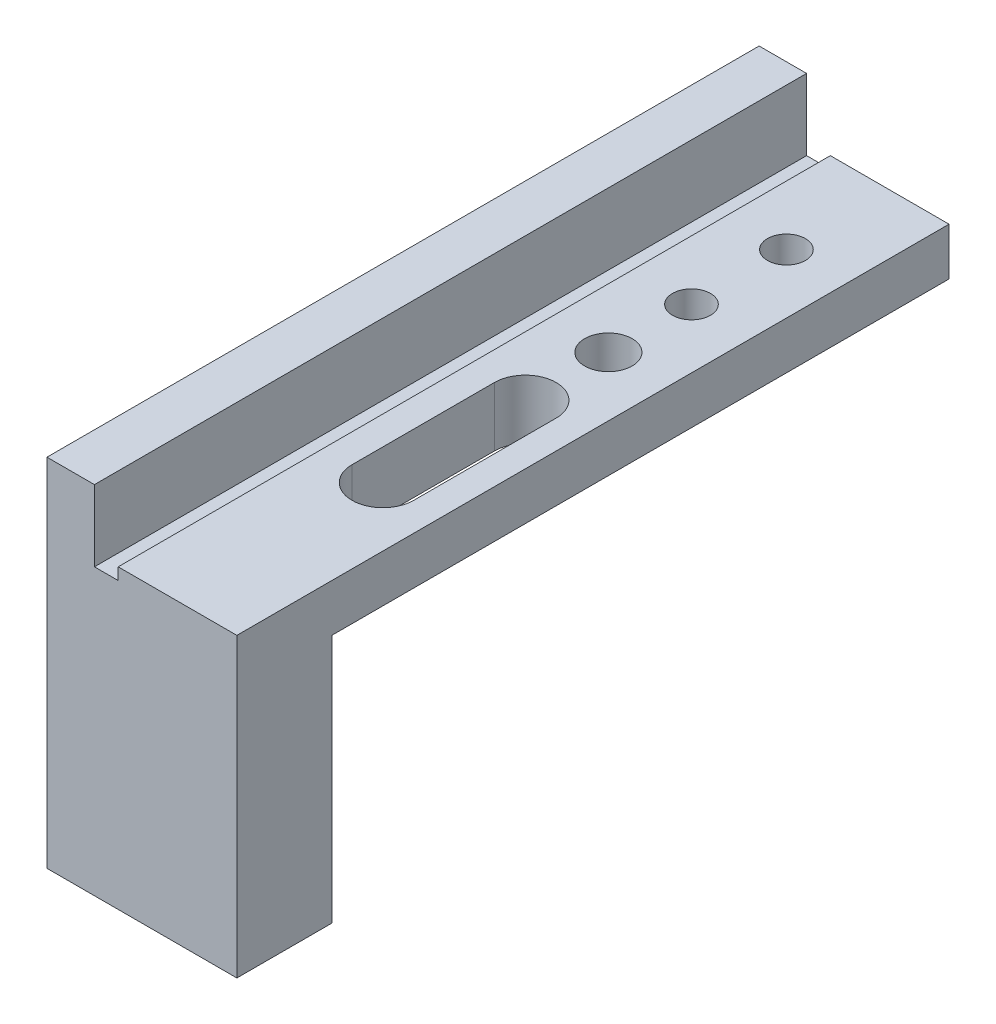
SolidWorks part; units mm, degrees
ref_plane "Front Plane" through (0, 0, 0) normal (0, 0, 1) x (1, 0, 0)
ref_plane "Top Plane" through (0, 0, 0) normal (0, 1, 0) x (1, 0, 0)
ref_plane "Right Plane" through (0, 0, 0) normal (1, 0, 0) x (0, 0, -1)
sketch "Sketch1" plane through (0, 0, 0) normal (0, 0, 1) x (1, 0, 0)
  line L1 (-5.1525, 3) -> (-3.1525, 3)
  line L2 (-5.1525, 3) -> (-5.1525, -2)
  line L4 (-3.1525, 3) -> (-3.1525, 0)
  line L5 (-5.1525, -2) -> (2.8475, -2)
  line L7 (-2.1525, 0.5) -> (2.8475, 0.5)
  line L8 (2.8475, -2) -> (2.8475, 0.5)
  line L9 (-3.1525, 0) -> (-2.1525, 0)
  line L10 (-2.1525, 0) -> (-2.1525, 0.5)
  dimension "D1" = 2
  dimension "D2" = 1
  dimension "D3" = 0.5
  dimension "D4" = 8
  dimension "D5" = 5
  dimension "D6" = 2.5
extrude "Boss-Extrude1" add sketch "Sketch1" along normal blind 30
sketch "Sketch2" plane through (0, -2, 0) normal (0, -1, 0) x (1, 0, 0)
  line L1 (-5.1525, 30) -> (-5.1525, 0) construction
  line L2 (2.8475, 30) -> (-5.1525, 30)
  line L3 (2.8475, 30) -> (2.8475, 26)
  line L4 (2.8475, 26) -> (-5.1525, 26)
  line L5 (-5.1525, 30) -> (-5.1525, 26)
  dimension "D1" = 4
sketch "Sketch3" plane through (0, 0.5, 0) normal (0, 1, 0) x (1, 0, 0)
  line L0 (0.3475, -21.35) -> (0.3475, -15.35) construction
  line L1 (-0.9525, -21.35) -> (-0.9525, -15.35)
  line L2 (1.6475, -21.35) -> (1.6475, -15.35)
  line L4 (-5.1525, -30) -> (-5.1525, 0) construction
  line L5 (2.8475, -30) -> (-2.1525, -30) construction
  circle A0 centre (0.3475, -11.85) radius 1
  arc A1 (-0.9525, -21.35) -> (1.6475, -21.35) centre (0.3475, -21.35) ccw
  arc A2 (1.6475, -15.35) -> (-0.9525, -15.35) centre (0.3475, -15.35) ccw
  point P4 (0.3475, -18.35)
  dimension "D2" = 1.3
  dimension "D6" = 2
  dimension "D1" = 6
  dimension "D3" = 8.65
  dimension "D4" = 5.5
  dimension "D5" = 18.15
extrude "Cut-Extrude1" cut sketch "Sketch3" against normal blind 10
hole_wizard "M2 Tapped Hole1" positions "Sketch4" profile "Sketch5" tap size "M2" standard "ISO"
sketch "Sketch4" plane through (0, 0.5, 0) normal (0, 1, 0) x (1, 0, 0)
  line L0 (-5.1525, -30) -> (-5.1525, 0) construction
  line L2 (2.8475, -30) -> (-2.1525, -30) construction
  point P0 (0.3475, -4.35)
  point P2 (0.3475, -8.35)
  dimension "D1" = 5.5
  dimension "D2" = 25.65
  dimension "D3" = 21.65
sketch "Sketch5" plane through (0.3475, 0.5, 4.35) normal (1, 0, 0) x (0, 0, 1)
  line L0 (0, 0) -> (0, 5.6807)
  line L1 (0, 5.6807) -> (0.8, 5.2)
  line L2 (0.8, 5.2) -> (0.8, 0)
  line L5 (0.8, 0) -> (0, 0)
  line L10 (0, 5.6807) -> (-0.8, 5.2) construction
  line L11 (0, -6.35) -> (0, 107.95) construction
  dimension "Tap Drill Dia." = 1.6
  dimension "Tap Drill Depth" = 5.2
  dimension "Drill Angle" = 118
cosmetic thread "Hole Thread2" parameters "D1"=2.5, "D2"=2
cosmetic thread "Hole Thread3" parameters "D1"=2.5, "D2"=2
extrude "Boss-Extrude2" add sketch "Sketch2" along normal blind 10
chamfer "Chamfer1" distance 0.5 angle 45 2 edges at (-5.1525, -2, 13) (2.8475, -2, 13)
